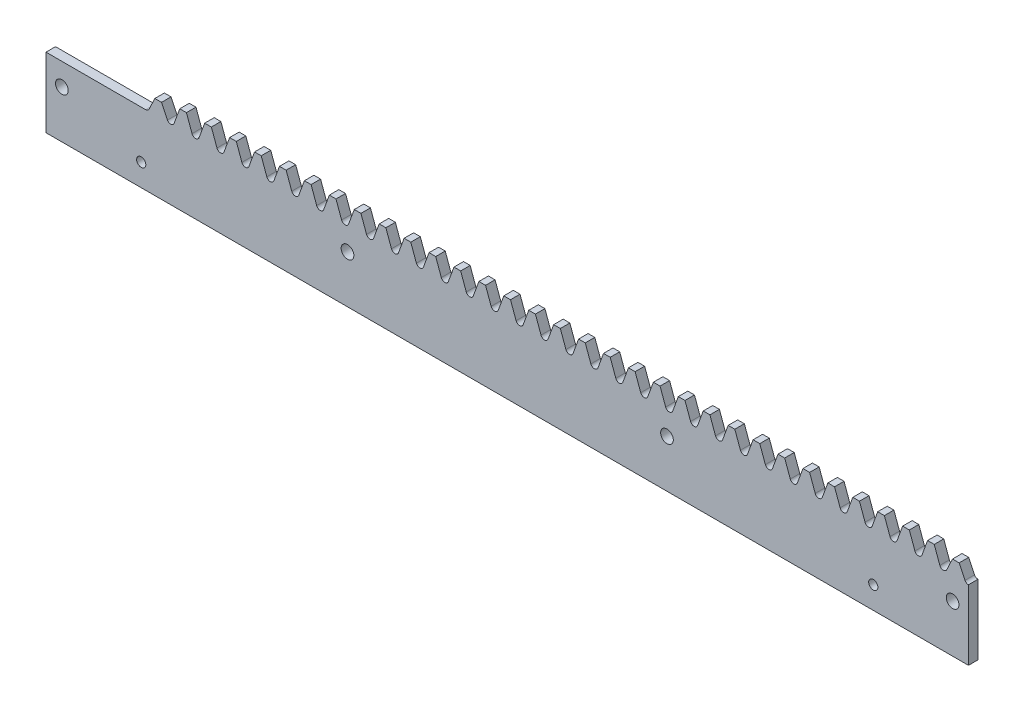
SolidWorks part; units mm, degrees
ref_plane "Plane1" through (0, 0, 0) normal (0, 0, 1) x (1, 0, 0)
ref_plane "Plane2" through (0, 0, 0) normal (0, 1, 0) x (1, 0, 0)
ref_plane "Plane3" through (0, 0, 0) normal (1, 0, 0) x (0, 0, -1)
sketch "Esquisse1" plane through (0, 0, 0) normal (0, 0, 1) x (1, 0, 0)
  line L0 (-11.781, 22) -> (19.635, 22)
  line L1 (23.5619, 29.1362) -> (23.5619, 19.2192) construction
  line L2 (-16.2297, 22) -> (24.6155, 22) construction
  line L3 (18.2522, 26.5) -> (283.3605, 26.5) construction
  line L4 (22.5084, 28.8854) -> (22.5084, 23.1798) construction
  line L5 (22.5084, 26.5) -> (20.6365, 22.5562)
  line L6 (24.6155, 26.5) -> (26.4874, 22.5562)
  line L8 (22.5084, 26.5) -> (24.6155, 26.5)
  line L10 (275.9429, 26.742) -> (275.9429, 19.9201) construction
  line L11 (273.8358, 26.742) -> (273.8358, 19.9201) construction
  line L12 (273.8358, 26.5) -> (272.0069, 22.6314)
  line L13 (275.9429, 26.5) -> (277.7718, 22.6314)
  line L14 (273.8358, 26.5) -> (275.9429, 26.5)
  line L20 (28.5976, 22.7763) -> (30.3624, 27.625)
  line L21 (30.3624, 27.625) -> (32.4695, 27.625)
  line L22 (34.2343, 22.7763) -> (32.4695, 27.625)
  line L23 (36.4515, 22.7763) -> (38.2163, 27.625)
  line L24 (38.2163, 27.625) -> (40.3235, 27.625)
  line L25 (42.0883, 22.7763) -> (40.3235, 27.625)
  line L26 (44.3055, 22.7763) -> (46.0703, 27.625)
  line L27 (46.0703, 27.625) -> (48.1775, 27.625)
  line L28 (49.9423, 22.7763) -> (48.1775, 27.625)
  line L29 (52.1595, 22.7763) -> (53.9243, 27.625)
  line L30 (53.9243, 27.625) -> (56.0314, 27.625)
  line L31 (57.7962, 22.7763) -> (56.0314, 27.625)
  line L32 (60.0135, 22.7763) -> (61.7783, 27.625)
  line L33 (61.7783, 27.625) -> (63.8854, 27.625)
  line L34 (65.6502, 22.7763) -> (63.8854, 27.625)
  line L35 (67.8675, 22.7763) -> (69.6323, 27.625)
  line L36 (69.6323, 27.625) -> (71.7394, 27.625)
  line L37 (73.5042, 22.7763) -> (71.7394, 27.625)
  line L38 (75.7215, 22.7763) -> (77.4862, 27.625)
  line L39 (77.4862, 27.625) -> (79.5934, 27.625)
  line L40 (81.3582, 22.7763) -> (79.5934, 27.625)
  line L41 (83.5754, 22.7763) -> (85.3402, 27.625)
  line L42 (85.3402, 27.625) -> (87.4474, 27.625)
  line L43 (89.2122, 22.7763) -> (87.4474, 27.625)
  line L44 (91.4294, 22.7763) -> (93.1942, 27.625)
  line L45 (93.1942, 27.625) -> (95.3013, 27.625)
  line L46 (97.0661, 22.7763) -> (95.3013, 27.625)
  line L47 (99.2834, 22.7763) -> (101.0482, 27.625)
  line L48 (101.0482, 27.625) -> (103.1553, 27.625)
  line L49 (104.9201, 22.7763) -> (103.1553, 27.625)
  line L50 (107.1374, 22.7763) -> (108.9022, 27.625)
  line L51 (108.9022, 27.625) -> (111.0093, 27.625)
  line L52 (112.7741, 22.7763) -> (111.0093, 27.625)
  line L53 (114.9914, 22.7763) -> (116.7562, 27.625)
  line L54 (116.7562, 27.625) -> (118.8633, 27.625)
  line L55 (120.6281, 22.7763) -> (118.8633, 27.625)
  line L56 (122.8453, 22.7763) -> (124.6101, 27.625)
  line L57 (124.6101, 27.625) -> (126.7173, 27.625)
  line L58 (128.4821, 22.7763) -> (126.7173, 27.625)
  line L59 (130.6993, 22.7763) -> (132.4641, 27.625)
  line L60 (132.4641, 27.625) -> (134.5713, 27.625)
  line L61 (136.3361, 22.7763) -> (134.5713, 27.625)
  line L62 (138.5533, 22.7763) -> (140.3181, 27.625)
  line L63 (140.3181, 27.625) -> (142.4252, 27.625)
  line L64 (144.19, 22.7763) -> (142.4252, 27.625)
  line L65 (146.4073, 22.7763) -> (148.1721, 27.625)
  line L66 (148.1721, 27.625) -> (150.2792, 27.625)
  line L67 (152.044, 22.7763) -> (150.2792, 27.625)
  line L68 (154.2613, 22.7763) -> (156.0261, 27.625)
  line L69 (156.0261, 27.625) -> (158.1332, 27.625)
  line L70 (159.898, 22.7763) -> (158.1332, 27.625)
  line L71 (162.1153, 22.7763) -> (163.88, 27.625)
  line L72 (163.88, 27.625) -> (165.9872, 27.625)
  line L73 (167.752, 22.7763) -> (165.9872, 27.625)
  line L74 (169.9692, 22.7763) -> (171.734, 27.625)
  line L75 (171.734, 27.625) -> (173.8412, 27.625)
  line L76 (175.606, 22.7763) -> (173.8412, 27.625)
  line L77 (177.8232, 22.7763) -> (179.588, 27.625)
  line L78 (179.588, 27.625) -> (181.6951, 27.625)
  line L79 (183.4599, 22.7763) -> (181.6951, 27.625)
  line L80 (185.6772, 22.7763) -> (187.442, 27.625)
  line L81 (187.442, 27.625) -> (189.5491, 27.625)
  line L82 (191.3139, 22.7763) -> (189.5491, 27.625)
  line L83 (193.5312, 22.7763) -> (195.296, 27.625)
  line L84 (195.296, 27.625) -> (197.4031, 27.625)
  line L85 (199.1679, 22.7763) -> (197.4031, 27.625)
  line L86 (201.3852, 22.7763) -> (203.15, 27.625)
  line L87 (203.15, 27.625) -> (205.2571, 27.625)
  line L88 (207.0219, 22.7763) -> (205.2571, 27.625)
  line L89 (209.2391, 22.7763) -> (211.0039, 27.625)
  line L90 (211.0039, 27.625) -> (213.1111, 27.625)
  line L91 (214.8759, 22.7763) -> (213.1111, 27.625)
  line L92 (217.0931, 22.7763) -> (218.8579, 27.625)
  line L93 (218.8579, 27.625) -> (220.9651, 27.625)
  line L94 (222.7298, 22.7763) -> (220.9651, 27.625)
  line L95 (224.9471, 22.7763) -> (226.7119, 27.625)
  line L96 (226.7119, 27.625) -> (228.819, 27.625)
  line L97 (230.5838, 22.7763) -> (228.819, 27.625)
  line L98 (232.8011, 22.7763) -> (234.5659, 27.625)
  line L99 (234.5659, 27.625) -> (236.673, 27.625)
  line L100 (238.4378, 22.7763) -> (236.673, 27.625)
  line L101 (240.6551, 22.7763) -> (242.4199, 27.625)
  line L102 (242.4199, 27.625) -> (244.527, 27.625)
  line L103 (246.2918, 22.7763) -> (244.527, 27.625)
  line L104 (248.509, 22.7763) -> (250.2738, 27.625)
  line L105 (250.2738, 27.625) -> (252.381, 27.625)
  line L106 (254.1458, 22.7763) -> (252.381, 27.625)
  line L107 (256.363, 22.7763) -> (258.1278, 27.625)
  line L108 (258.1278, 27.625) -> (260.235, 27.625)
  line L109 (261.9998, 22.7763) -> (260.235, 27.625)
  line L110 (264.217, 22.7763) -> (265.9818, 27.625)
  line L111 (265.9818, 27.625) -> (268.0889, 27.625)
  line L112 (269.8537, 22.7763) -> (268.0889, 27.625)
  line L114 (19.635, 37.0607) -> (19.635, -15.8181) construction
  line L115 (283.3605, 22) -> (228.0591, 22) construction
  line L118 (-11.781, 22) -> (-11.781, 0)
  line L121 (278.8759, 22.0015) -> (278.8759, 0)
  line L131 (278.8759, 0) -> (-11.781, 0)
  line L132 (133.5177, 28.2837) -> (133.5177, 9.5143) construction
  line L133 (130.5371, 22) -> (141.4123, 22) construction
  line L149 (273.8358, 27.625) -> (275.9429, 27.625) [skipped]
  line L150 (277.7077, 22.7763) -> (275.9429, 27.625) [skipped]
  line L151 (272.071, 22.7763) -> (273.8358, 27.625) [skipped]
  circle A0 centre (183.8759, 15) radius 2
  circle A1 centre (83.219, 15) radius 2
  arc A7 (19.635, 22) -> (20.6365, 22.5562) centre (19.635, 23.1798) ccw
  arc A8 (27.4889, 22) -> (26.4874, 22.5562) centre (27.4889, 23.1798) cw
  arc A9 (27.4889, 22) -> (28.5976, 22.7763) centre (27.4889, 23.1798) ccw
  arc A10 (35.3429, 22) -> (34.2343, 22.7763) centre (35.3429, 23.1798) cw
  arc A11 (35.3429, 22) -> (36.4515, 22.7763) centre (35.3429, 23.1798) ccw
  arc A12 (43.1969, 22) -> (42.0883, 22.7763) centre (43.1969, 23.1798) cw
  arc A13 (43.1969, 22) -> (44.3055, 22.7763) centre (43.1969, 23.1798) ccw
  arc A14 (51.0509, 22) -> (49.9423, 22.7763) centre (51.0509, 23.1798) cw
  arc A15 (51.0509, 22) -> (52.1595, 22.7763) centre (51.0509, 23.1798) ccw
  arc A16 (58.9049, 22) -> (57.7962, 22.7763) centre (58.9049, 23.1798) cw
  arc A17 (58.9049, 22) -> (60.0135, 22.7763) centre (58.9049, 23.1798) ccw
  arc A18 (66.7588, 22) -> (65.6502, 22.7763) centre (66.7588, 23.1798) cw
  arc A19 (66.7588, 22) -> (67.8675, 22.7763) centre (66.7588, 23.1798) ccw
  arc A20 (74.6128, 22) -> (73.5042, 22.7763) centre (74.6128, 23.1798) cw
  arc A21 (74.6128, 22) -> (75.7215, 22.7763) centre (74.6128, 23.1798) ccw
  arc A22 (82.4668, 22) -> (81.3582, 22.7763) centre (82.4668, 23.1798) cw
  arc A23 (82.4668, 22) -> (83.5754, 22.7763) centre (82.4668, 23.1798) ccw
  arc A24 (90.3208, 22) -> (89.2122, 22.7763) centre (90.3208, 23.1798) cw
  arc A25 (90.3208, 22) -> (91.4294, 22.7763) centre (90.3208, 23.1798) ccw
  arc A26 (98.1748, 22) -> (97.0661, 22.7763) centre (98.1748, 23.1798) cw
  arc A27 (98.1748, 22) -> (99.2834, 22.7763) centre (98.1748, 23.1798) ccw
  arc A28 (106.0288, 22) -> (104.9201, 22.7763) centre (106.0288, 23.1798) cw
  arc A29 (106.0288, 22) -> (107.1374, 22.7763) centre (106.0288, 23.1798) ccw
  arc A30 (113.8827, 22) -> (112.7741, 22.7763) centre (113.8827, 23.1798) cw
  arc A31 (113.8827, 22) -> (114.9914, 22.7763) centre (113.8827, 23.1798) ccw
  arc A32 (121.7367, 22) -> (120.6281, 22.7763) centre (121.7367, 23.1798) cw
  arc A33 (121.7367, 22) -> (122.8453, 22.7763) centre (121.7367, 23.1798) ccw
  arc A34 (129.5907, 22) -> (128.4821, 22.7763) centre (129.5907, 23.1798) cw
  arc A35 (129.5907, 22) -> (130.6993, 22.7763) centre (129.5907, 23.1798) ccw
  arc A36 (137.4447, 22) -> (136.3361, 22.7763) centre (137.4447, 23.1798) cw
  arc A37 (137.4447, 22) -> (138.5533, 22.7763) centre (137.4447, 23.1798) ccw
  arc A38 (145.2987, 22) -> (144.19, 22.7763) centre (145.2987, 23.1798) cw
  arc A39 (145.2987, 22) -> (146.4073, 22.7763) centre (145.2987, 23.1798) ccw
  arc A40 (153.1526, 22) -> (152.044, 22.7763) centre (153.1526, 23.1798) cw
  arc A41 (153.1526, 22) -> (154.2613, 22.7763) centre (153.1526, 23.1798) ccw
  arc A42 (161.0066, 22) -> (159.898, 22.7763) centre (161.0066, 23.1798) cw
  arc A43 (161.0066, 22) -> (162.1153, 22.7763) centre (161.0066, 23.1798) ccw
  arc A44 (168.8606, 22) -> (167.752, 22.7763) centre (168.8606, 23.1798) cw
  arc A45 (168.8606, 22) -> (169.9692, 22.7763) centre (168.8606, 23.1798) ccw
  arc A46 (176.7146, 22) -> (175.606, 22.7763) centre (176.7146, 23.1798) cw
  arc A47 (176.7146, 22) -> (177.8232, 22.7763) centre (176.7146, 23.1798) ccw
  arc A48 (184.5686, 22) -> (183.4599, 22.7763) centre (184.5686, 23.1798) cw
  arc A49 (184.5686, 22) -> (185.6772, 22.7763) centre (184.5686, 23.1798) ccw
  arc A50 (192.4226, 22) -> (191.3139, 22.7763) centre (192.4226, 23.1798) cw
  arc A51 (192.4226, 22) -> (193.5312, 22.7763) centre (192.4226, 23.1798) ccw
  arc A52 (200.2765, 22) -> (199.1679, 22.7763) centre (200.2765, 23.1798) cw
  arc A53 (200.2765, 22) -> (201.3852, 22.7763) centre (200.2765, 23.1798) ccw
  arc A54 (208.1305, 22) -> (207.0219, 22.7763) centre (208.1305, 23.1798) cw
  arc A55 (208.1305, 22) -> (209.2391, 22.7763) centre (208.1305, 23.1798) ccw
  arc A56 (215.9845, 22) -> (214.8759, 22.7763) centre (215.9845, 23.1798) cw
  arc A57 (215.9845, 22) -> (217.0931, 22.7763) centre (215.9845, 23.1798) ccw
  arc A58 (223.8385, 22) -> (222.7298, 22.7763) centre (223.8385, 23.1798) cw
  arc A59 (223.8385, 22) -> (224.9471, 22.7763) centre (223.8385, 23.1798) ccw
  arc A60 (231.6925, 22) -> (230.5838, 22.7763) centre (231.6925, 23.1798) cw
  arc A61 (231.6925, 22) -> (232.8011, 22.7763) centre (231.6925, 23.1798) ccw
  arc A62 (239.5464, 22) -> (238.4378, 22.7763) centre (239.5464, 23.1798) cw
  arc A63 (239.5464, 22) -> (240.6551, 22.7763) centre (239.5464, 23.1798) ccw
  arc A64 (247.4004, 22) -> (246.2918, 22.7763) centre (247.4004, 23.1798) cw
  arc A65 (247.4004, 22) -> (248.509, 22.7763) centre (247.4004, 23.1798) ccw
  arc A66 (255.2544, 22) -> (254.1458, 22.7763) centre (255.2544, 23.1798) cw
  arc A67 (255.2544, 22) -> (256.363, 22.7763) centre (255.2544, 23.1798) ccw
  arc A68 (263.1084, 22) -> (261.9998, 22.7763) centre (263.1084, 23.1798) cw
  arc A69 (263.1084, 22) -> (264.217, 22.7763) centre (263.1084, 23.1798) ccw
  arc A70 (270.9624, 22) -> (269.8537, 22.7763) centre (270.9624, 23.1798) cw
  arc A72 (270.9624, 22) -> (272.0069, 22.6314) centre (270.9624, 23.1798) ccw
  arc A79 (278.8759, 22.0015) -> (277.7718, 22.6314) centre (278.8163, 23.1798) cw
  circle A81 centre (-6.781, 15) radius 2
  circle A82 centre (273.8759, 15) radius 2
  dimension "D2" = 4.5
  dimension "D3" = 4
  dimension "D8" = 290.6568
  dimension "D9" = 90
  dimension "D10" = 5
  dimension "D11" = 90
  dimension "D7" = 5
  dimension "D12" = 100.6568
  dimension "D13" = 15
  dimension "D14" = 11.781
extrude "Extrusion1" add sketch "Esquisse1" along normal blind 3
sketch "Esquisse4" plane through (0, 0, 3) normal (0, 0, 1) x (1, 0, 0)
  line L0 (278.8759, 0) -> (-11.781, 0) construction
  line L1 (278.8759, 22.0015) -> (278.8759, 0) construction
  line L2 (-11.781, 22) -> (-11.781, 0) construction
  circle A0 centre (18.219, 7) radius 1.45
  circle A2 centre (248.8759, 7) radius 1.45
  dimension "D1" = 2.9
  dimension "D2" = 7
  dimension "D3" = 30
  dimension "D4" = 30
extrude "Enlèv. mat.-Extru.2" cut sketch "Esquisse4" against normal through all
